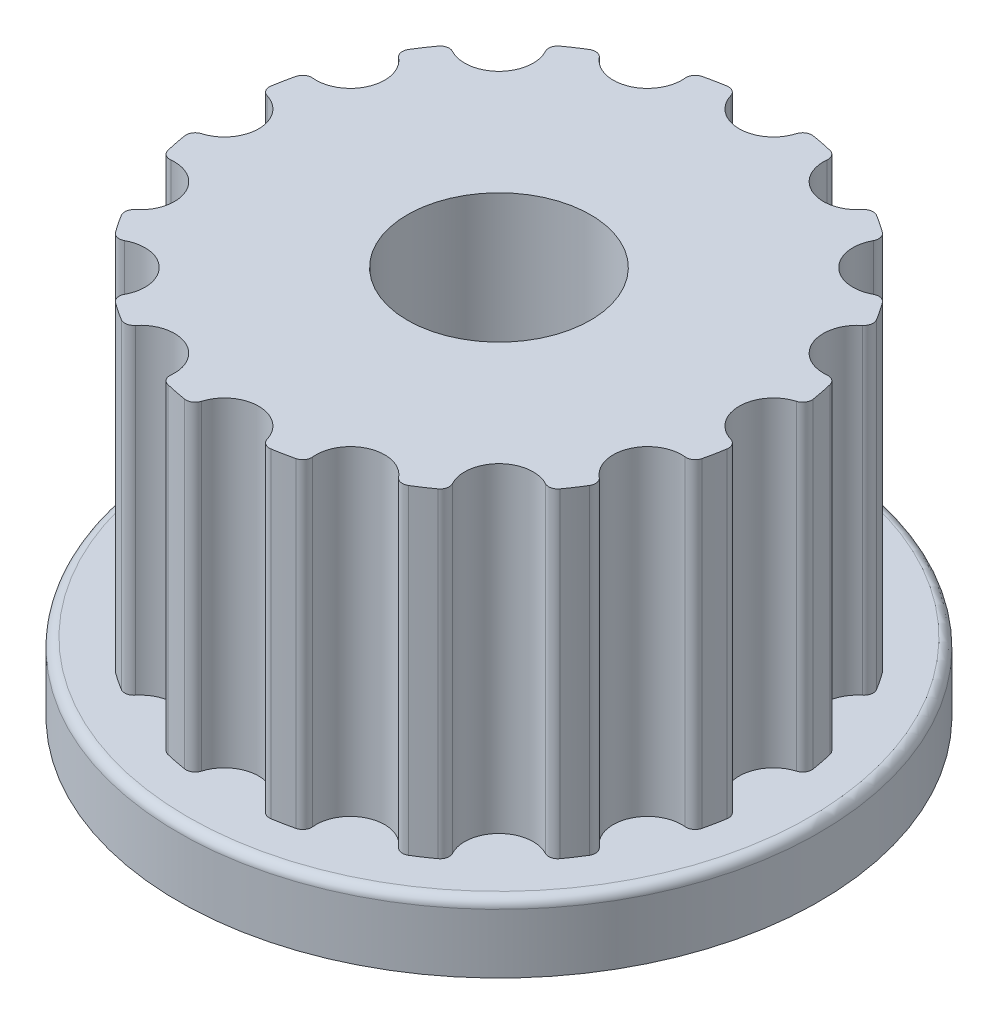
SolidWorks part; units mm, degrees
ref_plane "Front Plane" through (0, 0, 0) normal (0, 0, 1) x (1, 0, 0)
ref_plane "Top Plane" through (0, 0, 0) normal (0, 1, 0) x (1, 0, 0)
ref_plane "Right Plane" through (0, 0, 0) normal (1, 0, 0) x (0, 0, -1)
sketch "Sketch1" plane through (0, 0, 0) normal (0, 1, 0) x (1, 0, 0)
  circle A0 centre (0, 0) radius 6
  circle A1 centre (-6, 0) radius 0.75
  circle A2 centre (0, 0) radius 6
  circle A3 centre (-5.5433, 2.2961) radius 0.75
  circle A4 centre (0, 0) radius 6
  circle A5 centre (-4.2426, 4.2426) radius 0.75
  circle A6 centre (0, 0) radius 6
  circle A7 centre (-2.2961, 5.5433) radius 0.75
  circle A8 centre (0, 0) radius 6
  circle A9 centre (0, 6) radius 0.75
  circle A10 centre (0, 0) radius 6
  circle A11 centre (2.2961, 5.5433) radius 0.75
  circle A12 centre (0, 0) radius 6
  circle A13 centre (4.2426, 4.2426) radius 0.75
  circle A14 centre (0, 0) radius 6
  circle A15 centre (5.5433, 2.2961) radius 0.75
  circle A16 centre (0, 0) radius 6
  circle A17 centre (6, 0) radius 0.75
  circle A18 centre (0, 0) radius 6
  circle A19 centre (5.5433, -2.2961) radius 0.75
  circle A20 centre (0, 0) radius 6
  circle A21 centre (4.2426, -4.2426) radius 0.75
  circle A22 centre (0, 0) radius 6
  circle A23 centre (2.2961, -5.5433) radius 0.75
  circle A24 centre (0, 0) radius 6
  circle A25 centre (0, -6) radius 0.75
  circle A26 centre (0, 0) radius 6
  circle A27 centre (-2.2961, -5.5433) radius 0.75
  circle A28 centre (0, 0) radius 6
  circle A29 centre (-4.2426, -4.2426) radius 0.75
  circle A30 centre (0, 0) radius 6
  circle A31 centre (-5.5433, -2.2961) radius 0.75
extrude "Extrude7" add sketch "Sketch1" along normal blind 7 contours A31 A0 A29 A27 A25 A23 A21 A19 A17 A15 A13 A11 A9 A7 A5 A3 A1
sketch "Sketch3" plane through (0, 7, 0) normal (0, 1, 0) x (-1, 0, 0)
  circle A0 centre (0, 0) radius 2
sketch "Sketch4" plane through (0, 0, 0) normal (0, -1, 0) x (1, 0, 0)
  circle A0 centre (0, 0) radius 7
extrude "Extrude8" add sketch "Sketch4" along normal blind 1.5
extrude "Extrude9" cut sketch "Sketch3" against normal blind 8.5
fillet "Fillet3" radius 0.2 1 edges at (0, 0, -7)
fillet "Fillet4" radius 0.2 32 edges at (-5.7864, 3.5, -1.5866) (-5.2135, 3.5, -2.9697) (-4.7388, 3.5, -3.6802) (-3.6802, 3.5, -4.7388) (-2.9697, 3.5, -5.2135) (-1.5866, 3.5, -5.7864) (-0.7485, 3.5, -5.9531) (0.7485, 3.5, -5.9531) (1.5866, 3.5, -5.7864) (2.9697, 3.5, -5.2135) (3.6802, 3.5, -4.7388) (4.7388, 3.5, -3.6802) (5.2135, 3.5, -2.9697) (5.7864, 3.5, -1.5866) (5.9531, 3.5, -0.7485) (5.9531, 3.5, 0.7485) (5.7864, 3.5, 1.5866) (5.2135, 3.5, 2.9697) (4.7388, 3.5, 3.6802) (3.6802, 3.5, 4.7388) (2.9697, 3.5, 5.2135) (1.5866, 3.5, 5.7864) (0.7485, 3.5, 5.9531) (-0.7485, 3.5, 5.9531) (-1.5866, 3.5, 5.7864) (-2.9697, 3.5, 5.2135) (-3.6802, 3.5, 4.7388) (-4.7388, 3.5, 3.6802) (-5.2135, 3.5, 2.9697) (-5.7864, 3.5, 1.5866) (-5.9531, 3.5, 0.7485) (-5.9531, 3.5, -0.7485)
